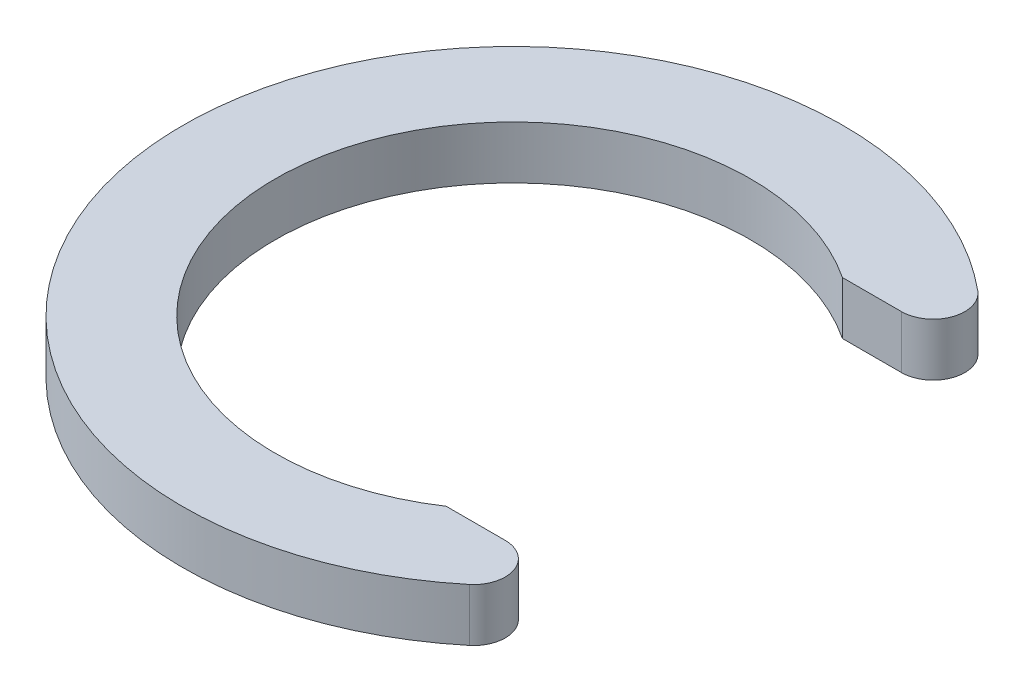
SolidWorks part; units mm, degrees
ref_plane "Front Plane" through (0, 0, 0) normal (0, 0, 1) x (1, 0, 0)
ref_plane "Top Plane" through (0, 0, 0) normal (0, 1, 0) x (1, 0, 0)
ref_plane "Right Plane" through (0, 0, 0) normal (1, 0, 0) x (0, 0, -1)
sketch "Sketch1" plane through (0, 0, 0) normal (0, 1, 0) x (1, 0, 0)
  line L0 (4.9749, 7.5) -> (10, 7.5)
  line L1 (4.9749, -7.5) -> (10, -7.5)
  arc A0 (10, 7.5) -> (10, -7.5) centre (0, 0) ccw
  arc A1 (4.9749, 7.5) -> (4.9749, -7.5) centre (0, 0) ccw
  dimension "D1" = 25
  dimension "D2" = 18
  dimension "D3" = 7.5
  dimension "D4" = 7.5
extrude "Boss-Extrude2" add sketch "Sketch1" along normal blind 2
fillet "Fillet1" radius 1.2 2 edges at (10, 1, -7.5) (10, 1, 7.5)
